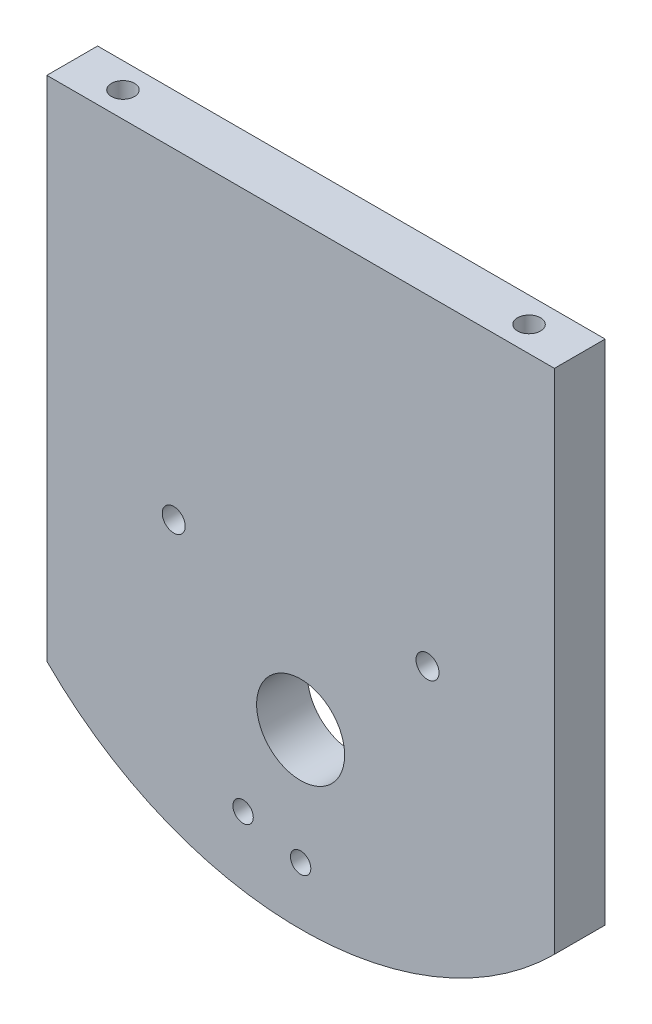
SolidWorks part; units mm, degrees
ref_plane "Front Plane" through (0, 0, 0) normal (0, 0, 1) x (1, 0, 0)
ref_plane "Top Plane" through (0, 0, 0) normal (0, 1, 0) x (1, 0, 0)
ref_plane "Right Plane" through (0, 0, 0) normal (1, 0, 0) x (0, 0, -1)
sketch "Sketch2" plane through (0, 0, 0) normal (0, 0, 1) x (1, 0, 0)
  line L1 (-75, -45) -> (75, -45)
  line L2 (-75, -45) -> (-75, 45)
  line L3 (-75, 45) -> (75, 45)
  line L4 (75, -45) -> (75, 45)
  line L5 (-75, -45) -> (75, 45) construction
  line L6 (-75, 45) -> (75, -45) construction
  line L7 (-75, -45) -> (75, -45)
  line L8 (-75, -45) -> (-75, -105)
  line L9 (-75, -105) -> (75, -105)
  line L10 (75, -45) -> (75, -105)
  arc A0 (-75, -105) -> (75, -105) centre (0, -30) ccw
  point P0 (0, 0)
  dimension "D1" = 150
  dimension "D2" = 90
  dimension "D3" = 60
extrude "Boss-Extrude1" add sketch "Sketch2" along normal blind 15 contours L1 L4 L3 L2 | L10 L1 L8 L9 | L9 A0
sketch "Sketch3" plane through (0, 0, 15) normal (0, 0, 1) x (1, 0, 0)
  line L0 (0, 45) -> (0, -136.066) construction
  line L1 (-75, 45) -> (75, 45) construction
  line L2 (-17, -114.4449) -> (0, -85) construction
  arc A0 (-75, -105) -> (75, -105) centre (0, -30) ccw construction
  circle A1 centre (0, -85) radius 13.005
  circle A2 centre (0, -85) radius 34
  circle A3 centre (-17, -114.4449) radius 3.01
  circle A4 centre (0, -119) radius 3.01
  point P10 (0, -119)
  point P11 (-17, -114.4449)
  dimension "D1" = 130
  dimension "D2" = 30
extrude "Cut-Extrude1" cut sketch "Sketch3" against normal through all contours A1 | A2 A4 | A2 A4 | A2 A3 | A2 A3
sketch "Sketch6" plane through (0, 0, 0) normal (0, 0, -1) x (-1, 0, 0)
  line L3 (-75, -105) -> (-75, 45) construction
  line L4 (75, -105) -> (75, 45) construction
  line L5 (75, 45) -> (-75, 45) construction
  line L6 (0, 45) -> (0, -136.066) construction
  line L7 (-75, -50) -> (75, -50) construction
  arc A0 (-75, -105) -> (75, -105) centre (0, -30) ccw construction
  point P0 (-37.5, -50)
  point P1 (37.5, -50)
  dimension "D1" = 37.5
  dimension "D2" = 95
  dimension "D3" = 37.5
sketch "Sketch9" plane through (0, 0, 15) normal (0, 0, 1) x (1, 0, 0)
  point P0 (-37.5, -50)
  point P1 (37.5, -50)
hole_wizard "Tap Drill for M8x1.25 Tap2" positions "Sketch11" profile "Sketch10" hole size "M8x1.25" standard "ANSI Metric"
sketch "Sketch11" plane through (0, 0, 15) normal (0, 0, 1) x (1, 0, 0)
  point P0 (-37.5, -50)
  point P3 (37.5, -50)
sketch "Sketch10" plane through (-37.5, -50, 15) normal (1, 0, 0) x (0, -1, 0)
  line L0 (0, 0) -> (0, 12.0429)
  line L1 (0, 12.0429) -> (3.4, 10)
  line L2 (3.4, 10) -> (3.4, 0)
  line L5 (3.4, 0) -> (0, 0)
  line L10 (0, 12.0429) -> (-3.4, 10) construction
  line L11 (0, -6.35) -> (0, 107.95) construction
  dimension "Hole Dia." = 6.8
  dimension "Hole Depth" = 10
  dimension "Drill Angle" = 118
sketch "Sketch12" plane through (0, 45, 0) normal (0, 1, 0) x (1, 0, 0)
  line L0 (-75, -7.5) -> (75, -7.5) construction
  line L1 (-75, -15) -> (-75, 0) construction
  line L2 (75, -15) -> (75, 0) construction
  line L3 (0, -14.5382) -> (0, 0) construction
  point P9 (-60, -7.5)
  point P10 (60, -7.5)
  dimension "D1" = 60
  dimension "D2" = 60
hole_wizard "Tap Drill for M8x1.25 Tap3" positions "Sketch14" profile "Sketch15" hole size "M8x1.25" standard "ANSI Metric"
sketch "Sketch14" plane through (0, 45, 0) normal (0, 1, 0) x (1, 0, 0)
  point P0 (-60, -7.5)
  point P3 (60, -7.5)
sketch "Sketch15" plane through (-60, 45, 7.5) normal (1, 0, 0) x (0, 0, 1)
  line L0 (0, 0) -> (0, 42.0429)
  line L1 (0, 42.0429) -> (3.4, 40)
  line L2 (3.4, 40) -> (3.4, 0)
  line L5 (3.4, 0) -> (0, 0)
  line L10 (0, 42.0429) -> (-3.4, 40) construction
  line L11 (0, -6.35) -> (0, 107.95) construction
  dimension "Hole Dia." = 6.8
  dimension "Hole Depth" = 40
  dimension "Drill Angle" = 118
